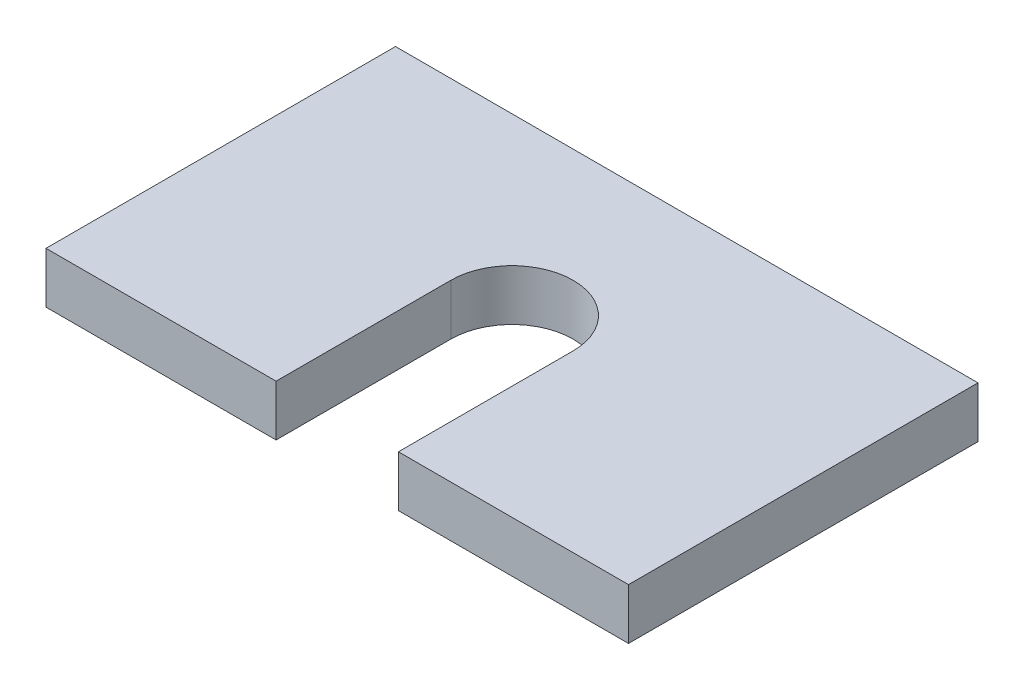
SolidWorks part; units mm, degrees
other "Markup1"
sketch "Sketch3" plane through (-63.5, 8.89, -38.1) normal (-0.9125, 0.4059, -0.0503) x (0.4069, 0.9134, -0.0121)
sketch "Sketch4" plane through (-63.5, 8.89, -38.1) normal (-0.9125, 0.4059, -0.0503) x (0.4069, 0.9134, -0.0121)
sketch "Sketch7" plane through (-63.5, 12.7, -38.1) normal (-0.9125, 0.4059, -0.0503) x (0.4069, 0.9134, -0.0121)
other "Markup2"
sketch "Sketch6" plane through (-63.5, 8.89, -38.1) normal (-0.9404, 0.2221, -0.2575) x (0.2799, 0.9357, -0.215)
sketch "Sketch8" plane through (-63.5, 12.7, -38.1) normal (-0.9404, 0.2221, -0.2575) x (0.2799, 0.9357, -0.215)
material "1060 Alloy"
ref_plane "Front Plane" through (0, 0, 0) normal (0, 0, 1) x (1, 0, 0)
ref_plane "Top Plane" through (0, 0, 0) normal (0, 1, 0) x (1, 0, 0)
ref_plane "Right Plane" through (0, 0, 0) normal (1, 0, 0) x (0, 0, -1)
sketch "Sketch1" plane through (0, 0, 0) normal (0, 1, 0) x (1, 0, 0)
  line L0 (-13.335, 0) -> (-13.335, -38.1)
  line L1 (63.5, 38.1) -> (-63.5, 38.1)
  line L2 (63.5, 38.1) -> (63.5, -38.1)
  line L3 (63.5, -38.1) -> (-63.5, -38.1)
  line L4 (-63.5, 38.1) -> (-63.5, -38.1)
  line L5 (63.5, 38.1) -> (-63.5, -38.1) construction
  line L6 (63.5, -38.1) -> (-63.5, 38.1) construction
  line L7 (13.335, 0) -> (13.335, -38.1)
  circle A0 centre (0, 0) radius 13.335
  point P0 (0, 0)
  dimension "D3" = 26.67
  dimension "D1" = 127
  dimension "D2" = 76.2
extrude "Boss-Extrude1" add sketch "Sketch1" along normal blind 11.1125 contours A0 L7 L3 L2 L1 L4 L0
sketch "Sketch5" plane through (0, 0, 0) normal (0, 1, 0) x (1, 0, 0)
  line L0 (0, 0) -> (75.1377, 0) construction
  line L1 (0, 0) -> (0, -44.5309) construction
